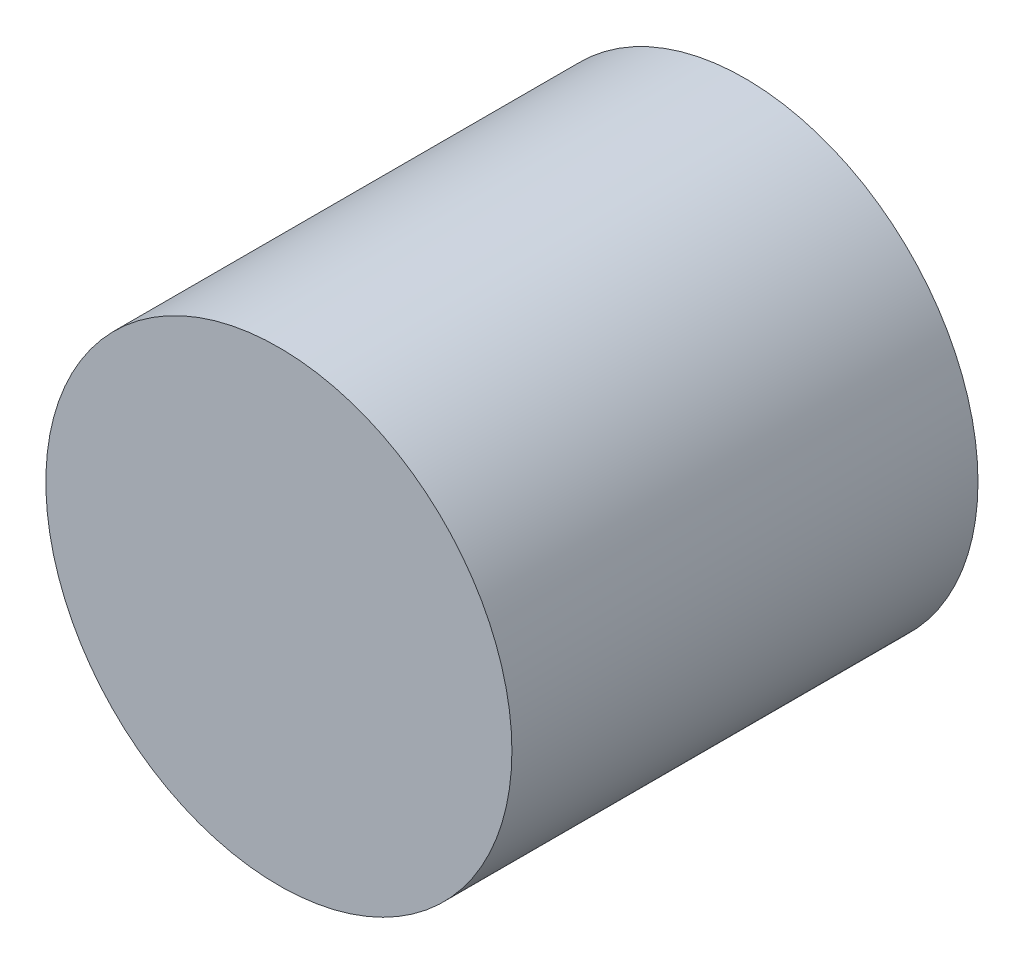
SolidWorks part; units mm, degrees
ref_plane "Ebene vorne" through (0, 0, 0) normal (0, 0, 1) x (1, 0, 0)
ref_plane "Ebene oben" through (0, 0, 0) normal (0, 1, 0) x (1, 0, 0)
ref_plane "Ebene rechts" through (0, 0, 0) normal (1, 0, 0) x (0, 0, -1)
sketch "Holes" plane through (0, 0, 0) normal (0, 0, 1) x (1, 0, 0)
  circle A0 centre (0, 680) radius 3.25
  circle A1 centre (70, 680) radius 3.25
sketch "Thickness" plane through (0, 0, 0) normal (1, 0, 0) x (0, 0, -1)
  line L0 (3, 680) -> (-3, 680)
  point P7 (0, 680)
sketch "Baseplate" plane through (0, 0, 0) normal (0, 0, 1) x (1, 0, 0)
  line L1 (-12.6, 640) -> (23.35, 640)
  line L2 (-12.6, 640) -> (-12.6, 634)
  line L3 (-12.6, 634) -> (23.35, 634)
  line L4 (23.35, 640) -> (23.35, 634)
  line L5 (-12.6, 637) -> (23.35, 637) construction
  circle A0 centre (19.35, 637) radius 1.25
  circle A1 centre (-8, 637) radius 1.25
sketch "Skizze4" plane through (0, 0, 0) normal (0, 0, 1) x (1, 0, 0)
  line L0 (-10, 610) -> (-10, 640)
  line L1 (-10, 640) -> (10, 640)
  line L2 (10, 640) -> (10, 610)
  line L3 (-10, 610) -> (-10, 688)
  line L4 (-10, 688) -> (10, 688)
  line L5 (10, 688) -> (10, 610)
  circle A1 centre (0, 680) radius 3
  point P10 (0, 0)
  dimension "D1" = 20
  dimension "D2" = 8
extrude "Aufsatz-Linear austragen1" add sketch "Skizze4" along normal up to vertex (3 mm away) and the other way up to vertex (3 mm away) contours L2 L5 L4 L3 L0 L1 | A1
